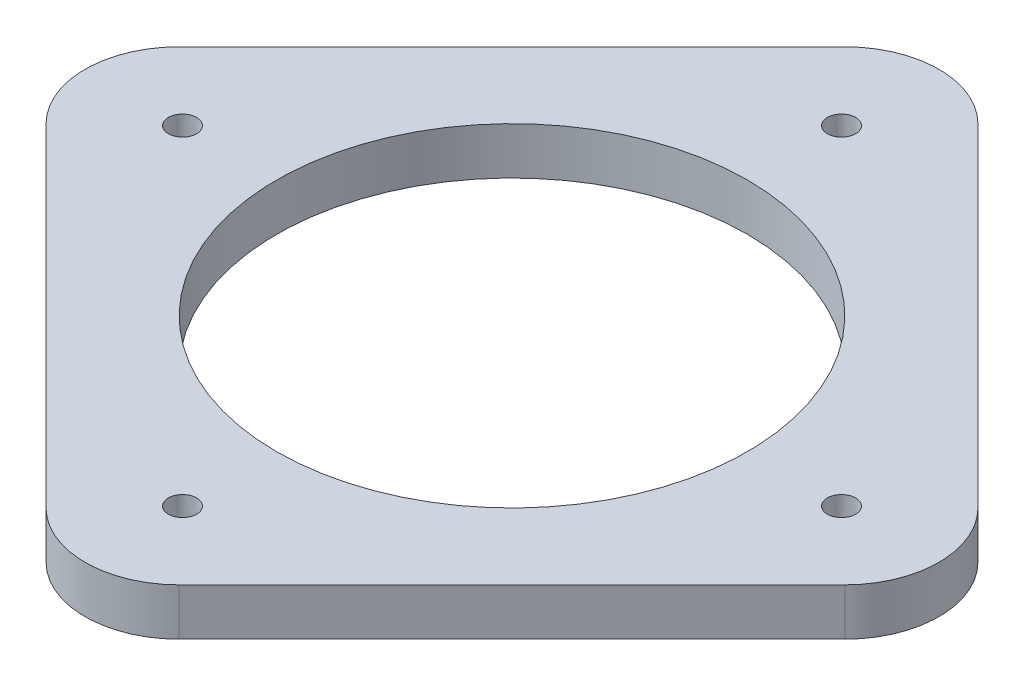
SolidWorks part; units mm, degrees
ref_plane "Alzado" through (0, 0, 0) normal (0, 0, 1) x (1, 0, 0)
ref_plane "Planta" through (0, 0, 0) normal (0, 1, 0) x (1, 0, 0)
ref_plane "Vista lateral" through (0, 0, 0) normal (1, 0, 0) x (0, 0, -1)
sketch "Croquis1" plane through (0, 0, 0) normal (0, 1, 0) x (1, 0, 0)
  line L0 (0, 0) -> (-49.4975, 0) construction
  line L1 (-42.4264, -7.0711) -> (-7.0711, -42.4264)
  line L2 (7.0711, -42.4264) -> (42.4264, -7.0711)
  line L3 (42.4264, 7.0711) -> (7.0711, 42.4264)
  line L4 (-7.0711, 42.4264) -> (-42.4264, 7.0711)
  line L5 (0, 0) -> (35, 0) construction
  circle A0 centre (0, 0) radius 25
  circle A1 centre (0, 0) radius 35 construction
  circle A2 centre (35, 0) radius 1.5
  arc A3 (-7.0711, -42.4264) -> (7.0711, -42.4264) centre (0, -35.3553) ccw
  arc A4 (-42.4264, -7.0711) -> (-42.4264, 7.0711) centre (-35.3553, 0) cw
  arc A5 (7.0711, 42.4264) -> (-7.0711, 42.4264) centre (0, 35.3553) ccw
  arc A6 (42.4264, -7.0711) -> (42.4264, 7.0711) centre (35.3553, 0) ccw
  circle A7 centre (0, -35) radius 1.5
  circle A8 centre (-35, 0) radius 1.5
  circle A9 centre (0, 35) radius 1.5
  point P19 (49.4975, 0)
  point P20 (-24.7487, 24.7487)
  point P29 (0, 0)
  dimension "D1" = 50
  dimension "D4" = 3
  dimension "D5" = 10
  dimension "D2" = 35
  dimension "D3" = 35
  dimension "D6" = 4
extrude "Saliente-Extruir1" add sketch "Croquis1" along normal blind 5
